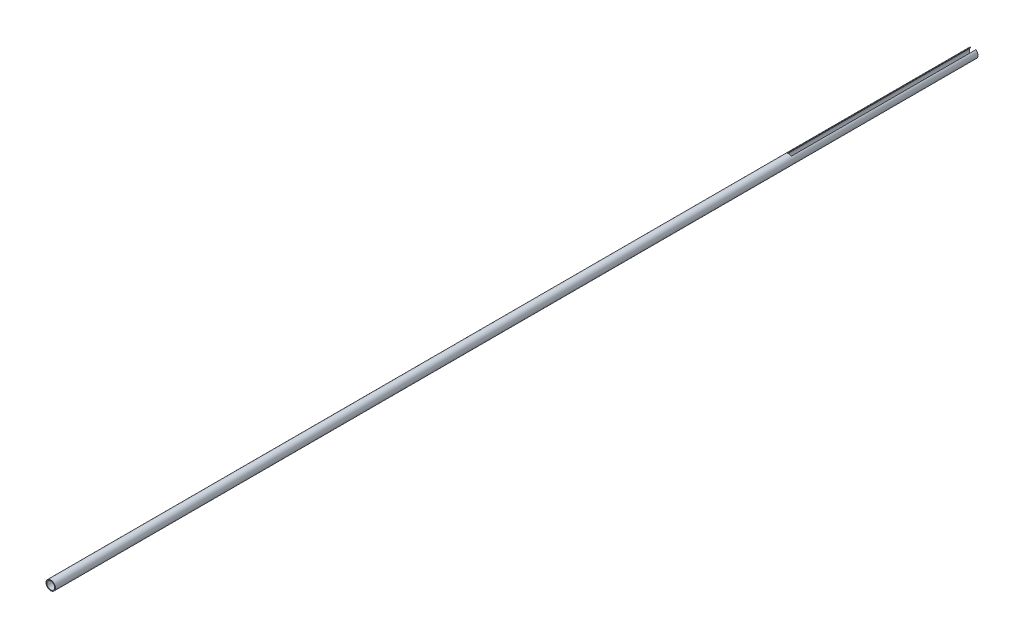
SolidWorks part; units mm, degrees
ref_plane "Front" through (0, 0, 0) normal (0, 0, 1) x (1, 0, 0)
ref_plane "Top" through (0, 0, 0) normal (0, 1, 0) x (1, 0, 0)
ref_plane "Right" through (0, 0, 0) normal (1, 0, 0) x (0, 0, -1)
sketch "Sketch1" plane through (0, 0, 0) normal (0, 0, 1) x (1, 0, 0)
  circle A0 centre (0, 0) radius 0.635
  circle A1 centre (0, 0) radius 0.5334
  dimension "D1" = 1.27
  dimension "D2" = 1.0668
extrude "Boss-Extrude1" add sketch "Sketch1" along normal blind 125
sketch "Sketch2" plane through (0, 0, 0) normal (0, 0, 1) x (1, 0, 0)
  line L1 (0.35, 0.1) -> (-0.35, 0.1)
  line L2 (0.35, 0.1) -> (0.35, 0.9668)
  line L3 (0.35, 0.9668) -> (-0.35, 0.9668)
  line L4 (-0.35, 0.1) -> (-0.35, 0.9668)
  line L5 (0.35, 0.1) -> (-0.35, 0.9668) construction
  line L6 (0.35, 0.9668) -> (-0.35, 0.1) construction
  circle A1 centre (0, 0) radius 0.5334 construction
  point P0 (0, 0.5334)
  dimension "D1" = 0.7
  dimension "D2" = 0.1
extrude "Cut-Extrude1" cut sketch "Sketch2" along normal blind 25
ref_point "Point1"
